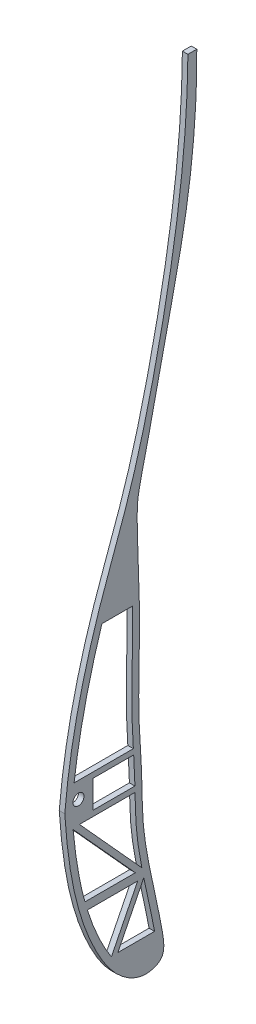
SolidWorks part; units mm, degrees
ref_plane "Front Plane" through (0, 0, 0) normal (0, 0, 1) x (1, 0, 0)
ref_plane "Top Plane" through (0, 0, 0) normal (0, 1, 0) x (1, 0, 0)
ref_plane "Right Plane" through (0, 0, 0) normal (1, 0, 0) x (0, 0, -1)
sketch "rib1" plane through (0, 0, 0) normal (1, 0, 0) x (0, 0, -1)
  line L0 (-71.2313, 531.3367) -> (928.7687, 531.3367) construction
  line L1 (884.1904, 599.9039) -> (887.9745, 599.9039)
  line L2 (856.9345, 370.6416) -> (865.0745, 370.6416)
  line L3 (850.4345, 376.6416) -> (850.4345, 379.6416)
  line L4 (850.4345, 376.6416) -> (850.4345, 373.6416)
  line L8 (855.8579, 382.6416) -> (843.7452, 382.6416)
  line L9 (855.8579, 382.6416) -> (864.8136, 382.6416)
  line L10 (856.9345, 368.6416) -> (844.7619, 368.6416)
  line L11 (856.9345, 368.6416) -> (865.1127, 368.6416)
  line L12 (866.2204, 340.1291) -> (848.917, 340.1291)
  line L13 (858.3122, 320.8088) -> (858.0269, 320.2668)
  line L14 (848.4203, 343.1291) -> (847.9481, 343.1291)
  line L15 (860.5104, 442.9155) -> (866.5886, 442.9155)
  line L16 (858.0269, 320.2668) -> (873.8862, 320.2668)
  line L17 (855.8579, 318.9992) -> (874.2194, 327.9134) construction
  line L18 (854.766, 321.2482) -> (871.1797, 329.2167) construction
  line L19 (871.1797, 329.2167) -> (873.8862, 320.2668)
  line L20 (843.5049, 367.0528) -> (865.4106, 343.1291)
  line L21 (866.2204, 340.1291) -> (856.8415, 322.3087)
  line L22 (844.7619, 368.6416) -> (867.7752, 343.5082)
  line L23 (868.4574, 340.0851) -> (858.3122, 320.8088)
  line L24 (865.4106, 343.1291) -> (848.4203, 343.1291)
  line L26 (856.9345, 370.6416) -> (850.4345, 370.6416)
  line L27 (850.4345, 370.6416) -> (850.4345, 373.6416)
  line L29 (855.8579, 380.6416) -> (864.9113, 380.6416)
  line L30 (855.8579, 380.6416) -> (850.4345, 380.6416)
  line L31 (850.4345, 380.6416) -> (850.4345, 379.6416)
  circle A0 centre (845.5789, 376.6416) radius 2
  arc A1 (841.0443, 380.5713) -> (847.6718, 415.72) centre (1017.3451, 365.528) cw
  arc A2 (851.2954, 425.5507) -> (861.6081, 456.6454) centre (699.0135, 493.3134) ccw
  arc A3 (862.9829, 461.9026) -> (884.1904, 599.9039) centre (374.0528, 607.6697) ccw
  arc A4 (840.7788, 371.8072) -> (855.8579, 318.9992) centre (950.1899, 374.4922) ccw
  arc A5 (867.6216, 376.9662) -> (872.8022, 332.64) centre (1022.9399, 372.6533) ccw
  arc A6 (867.6216, 376.9662) -> (871.4996, 461.3529) centre (1263.0251, 401.0778) cw
  arc A7 (871.9368, 463.9152) -> (887.9745, 599.9039) centre (-120.6116, 649.9108) ccw
  arc A8 (874.2194, 327.9134) -> (872.8022, 332.64) centre (950.104, 353.2418) cw
  arc A9 (841.0443, 380.5713) -> (840.7788, 371.8072) centre (920.7547, 373.7698) ccw
  arc A10 (851.2954, 425.5507) -> (847.6718, 415.72) centre (924.3857, 393.0268) ccw
  arc A11 (862.9829, 461.9026) -> (861.6081, 456.6454) centre (939.6482, 439.046) ccw
  arc A12 (871.4996, 461.3529) -> (871.9368, 463.9152) centre (950.5681, 449.1804) cw
  arc A13 (843.7452, 382.6416) -> (850.0691, 415.0108) centre (1017.3451, 365.528) cw
  arc A14 (853.5794, 424.5344) -> (850.0691, 415.0108) centre (924.3857, 393.0268) ccw
  arc A15 (853.5794, 424.5344) -> (860.5104, 442.9155) centre (699.0135, 493.3134) ccw
  arc A16 (843.5353, 380.3587) -> (850.0691, 415.0108) centre (1017.3451, 365.528) cw construction
  arc A17 (843.5049, 367.0528) -> (847.9481, 343.1291) centre (950.1899, 374.4922) ccw
  arc A18 (865.0721, 374.4641) -> (865.0745, 370.6416) centre (1022.9399, 372.6533) ccw
  arc A19 (864.962, 379.6766) -> (864.9113, 380.6416) centre (1263.0251, 401.0778) cw
  arc A20 (871.1797, 329.2167) -> (870.3865, 331.9962) centre (950.104, 353.2418) cw
  arc A21 (868.4574, 340.0851) -> (870.3865, 331.9962) centre (1022.9399, 372.6533) ccw
  arc A22 (865.3787, 461.1883) -> (886.6901, 599.8658) centre (374.0528, 607.6697) ccw construction
  arc A23 (865.1195, 376.9245) -> (870.3865, 331.9962) centre (1022.9399, 372.6533) ccw construction
  arc A24 (869.4795, 464.3757) -> (885.4776, 600.0277) centre (-120.6116, 649.9108) ccw construction
  arc A25 (843.278, 371.8685) -> (858.0127, 320.2668) centre (950.1899, 374.4922) ccw construction
  arc A26 (853.5794, 424.5344) -> (864.0469, 456.0955) centre (699.0135, 493.3134) ccw construction
  arc A27 (865.3787, 461.1883) -> (864.0469, 456.0955) centre (939.6482, 439.046) ccw construction
  arc A28 (865.1195, 376.9245) -> (869.0287, 461.7333) centre (1263.0251, 401.0778) cw construction
  arc A29 (869.0287, 461.7333) -> (869.4795, 464.3757) centre (950.5681, 449.1804) cw construction
  arc A30 (848.917, 340.1291) -> (856.8415, 322.3087) centre (950.1899, 374.4922) ccw
  arc A31 (865.1127, 368.6416) -> (867.7752, 343.5082) centre (1022.9399, 372.6533) ccw
  arc A32 (864.8136, 382.6416) -> (866.5886, 442.9155) centre (1263.0251, 401.0778) cw
  arc A33 (865.0721, 374.4641) -> (864.962, 379.6766) centre (785.0773, 375.3817) ccw
  spline S0 degree 3 poles (855.8579, 318.9992) (859.3648, 313.0596) (867.0534, 309.8477) (875.8907, 311.5767) (877.0472, 317.8757) (875.7309, 323.2627) (874.9921, 325.5984) (874.2194, 327.9134) knots 0 0 0 0 0.275026 0.518183 0.708506 0.751927 0.952395 0.952395 0.952395 0.952395
  dimension "D2" = 2.5
  dimension "D1" = 1000
sketch "rib2" plane through (0, 0, 0) normal (1, 0, 0) x (0, 0, -1)
  line L0 (-154.4211, 376.6416) -> (49845.5789, 376.6416) construction
  line L1 (-144.1421, 380.6416) -> (49855.8579, 380.6416) construction
  line L2 (-143.0655, 370.6416) -> (49856.9345, 370.6416) construction
  line L3 (782.8933, 343.3859) -> (760.3563, 368.2109)
  line L4 (-143.0655, 368.6416) -> (49856.9345, 368.6416) construction
  line L5 (-144.1421, 382.6416) -> (49855.8579, 382.6416) construction
  line L6 (785.2354, 343.762) -> (762.6647, 368.6416)
  line L7 (764.6298, 343.3859) -> (782.8933, 343.3859)
  line L8 (783.7374, 340.3859) -> (774.2204, 321.3554)
  line L9 (767.5719, 380.6416) -> (767.5719, 370.6416)
  line L10 (767.5719, 370.6416) -> (782.7291, 370.6416)
  line L11 (767.5719, 380.6416) -> (782.2855, 380.6416)
  line L12 (765.5126, 340.3859) -> (783.7374, 340.3859)
  line L13 (762.6647, 368.6416) -> (782.7755, 368.6416)
  line L14 (776.5435, 321.5294) -> (789.8459, 321.5294)
  line L15 (760.7138, 382.6416) -> (782.1585, 382.6416)
  line L16 (770.7866, 427.4918) -> (781.8144, 427.4918)
  line L17 (801.9062, 590.4081) -> (805.115, 590.4081)
  line L20 (785.9296, 340.298) -> (776.5435, 321.5294)
  circle A0 centre (762.2895, 376.6416) radius 2
  spline S0 degree 3 poles (757.3342, 374.654) (758.4886, 357.6416) (761.828, 335.0381) (776.3644, 313.1833) (785.8807, 308.842) (791.3139, 310.6103) (793.0754, 312.9879) (793.3375, 316.1077) (791.0414, 329.6431) (787.956, 341.1966) (785.2042, 359.6207) (785.4538, 372.9971) (783.4315, 397.4301) (785.2476, 420.7625) (783.0535, 455.8097) (784.4694, 464.3867) (788.1328, 479.2935) (793.2428, 503.9805) (802.5401, 542.6054) (805.2587, 572.3941) (805.115, 590.4081) knots 0 0 0 0 0.100348 0.1322 0.149146 0.158796 0.160734 0.16766 0.175847 0.234409 0.24607 0.285136 0.310616 0.385264 0.441942 0.454033 0.506165 0.624061 0.777474 1 1 1 1
  spline S1 degree 3 poles (801.9062, 590.4081) (801.6966, 560.1521) (794.9987, 516.4372) (781.937, 464.9222) (766.0277, 424.3103) (759.1775, 395.3186) (757.3342, 374.654) knots 0 0 0 0 0.408826 0.598518 0.719267 1 1 1 1
  spline S2 degree 3 poles (760.3563, 368.2109) (760.6455, 365.1083) (761.2971, 359.3998) (762.6856, 351.2079) (763.8909, 346.0643) (764.604, 343.4789) (764.6298, 343.3859) knots 0.01313 0.01313 0.01313 0.01313 0.031626 0.047245 0.062864 0.063447 0.063447 0.063447 0.063447
  spline S3 degree 3 poles (765.5126, 340.3859) (765.9421, 339.0082) (767.2255, 335.1967) (769.2617, 330.2911) (771.6089, 325.6402) (773.0967, 323.06) (774.0043, 321.6748) (774.2204, 321.3554) knots 0.069751 0.069751 0.069751 0.069751 0.078483 0.094102 0.101912 0.109721 0.112105 0.112105 0.112105 0.112105
  spline S5 degree 3 poles (782.7291, 370.6416) (782.7064, 371.5634) (782.6438, 373.8426) (782.4996, 377.1608) (782.3523, 379.5799) (782.2855, 380.6416) knots 0.276245 0.276245 0.276245 0.276245 0.281529 0.289339 0.295445 0.295445 0.295445 0.295445
  spline S6 degree 3 poles (789.8459, 321.5294) (789.8142, 321.6995) (789.7504, 322.0389) (789.4577, 323.5807) (788.9295, 326.2404) (788.1496, 329.9526) (787.3325, 333.724) (786.5882, 337.1579) (786.1256, 339.3494) (785.9296, 340.298) knots 0.178918 0.178918 0.178918 0.178918 0.179894 0.18087 0.187816 0.195625 0.203435 0.211244 0.21717 0.21717 0.21717 0.21717
  spline S7 degree 3 poles (785.2354, 343.762) (784.9117, 345.4358) (784.3695, 348.4126) (783.6834, 352.846) (783.0923, 358.3507) (782.8866, 363.6197) (782.8011, 367.501) (782.7755, 368.6416) knots 0.224345 0.224345 0.224345 0.224345 0.234672 0.242482 0.250291 0.26591 0.27243 0.27243 0.27243 0.27243
  spline S8 degree 3 poles (782.1585, 382.6416) (782.0098, 384.985) (781.5323, 392.7288) (781.6016, 402.5045) (781.8121, 413.0284) (781.8895, 420.0466) (781.8563, 425.0079) (781.8229, 427.0307) (781.8144, 427.4918) knots 0.299279 0.299279 0.299279 0.299279 0.312767 0.344005 0.359624 0.375243 0.383052 0.385336 0.385336 0.385336 0.385336
  spline S9 degree 3 poles (770.7866, 427.4918) (769.4671, 423.3387) (766.9647, 414.7701) (763.3804, 399.8515) (761.5251, 389.0141) (760.7138, 382.6416) knots 0.752168 0.752168 0.752168 0.752168 0.811773 0.874217 0.962264 0.962264 0.962264 0.962264
  point P26 (765.5126, 340.3859)
  point P30 (764.6298, 343.3859)
  point P35 (774.2204, 321.3554)
  point P36 (789.8459, 321.5294)
  point P37 (785.9296, 340.298)
  point P39 (760.3563, 368.2109)
  point P40 (760.0729, 371.4986)
extrude "Boss-Extrude1" add sketch "rib2" along normal blind 2
equation "\"1000mmm\"=767.321"
